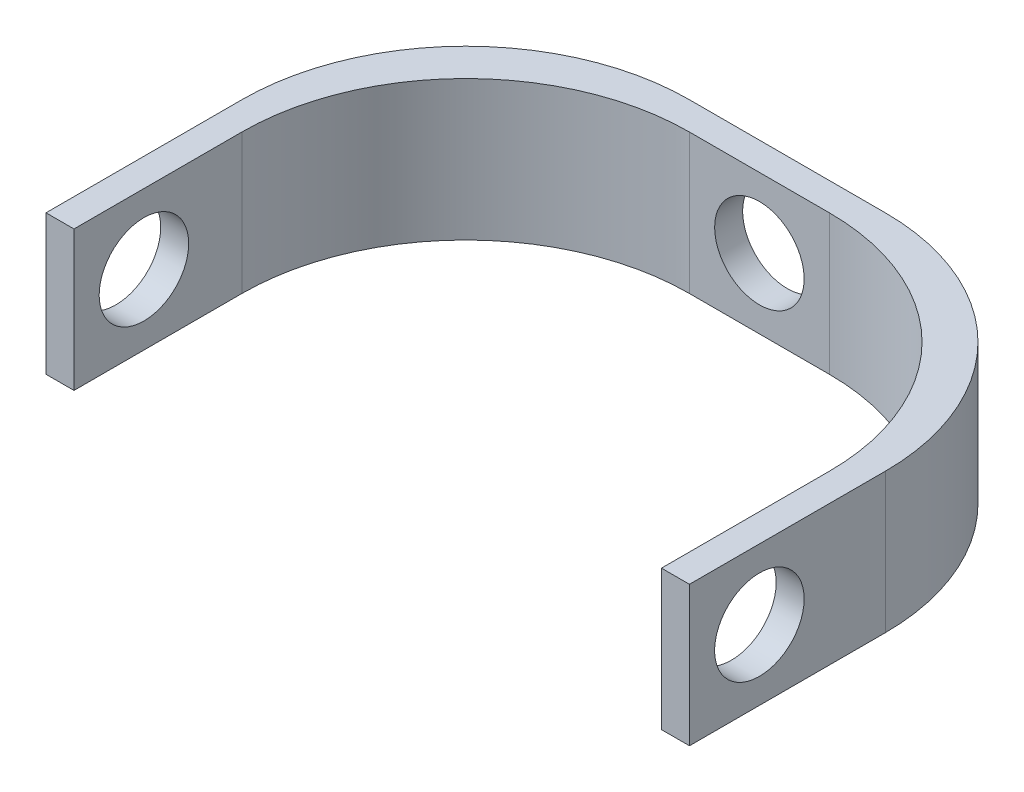
SolidWorks part; units mm, degrees
ref_plane "Front Plane" through (0, 0, 0) normal (0, 0, 1) x (1, 0, 0)
ref_plane "Top Plane" through (0, 0, 0) normal (0, 1, 0) x (1, 0, 0)
ref_plane "Right Plane" through (0, 0, 0) normal (1, 0, 0) x (0, 0, -1)
sketch "Sketch1" plane through (0, 0, 0) normal (0, 1, 0) x (1, 0, 0)
  line L0 (0, 0) -> (1, 0)
  line L1 (0, 0) -> (0, 15)
  line L2 (22, 0) -> (23, 0)
  line L3 (23, 0) -> (23, 15)
  line L4 (1, 14) -> (1, 0)
  line L5 (22, 14) -> (22, 0)
  line L6 (0, 15) -> (23, 15)
  line L7 (1, 14) -> (22, 14)
extrude "Boss-Extrude1" add sketch "Sketch1" along normal blind 5
sketch "Sketch2" plane through (0, 0, -15) normal (0, 0, -1) x (-1, 0, 0)
  circle A0 centre (-11.5, 2.5) radius 1.6
extrude "Cut-Extrude1" cut sketch "Sketch2" against normal blind 5
sketch "Sketch3" plane through (23, 0, 0) normal (1, 0, 0) x (0, 0, -1)
  line L0 (0, 5) -> (5, 5)
  line L1 (0, 5) -> (15, 5) construction
  circle A0 centre (2.5, 2.5) radius 1.6
extrude "Cut-Extrude2" cut sketch "Sketch3" against normal blind 27 contours A0
fillet "Fillet1" radius 8 4 edges at (23, 2.5, -15) (0, 2.5, -15) (1, 2.5, -14) (22, 2.5, -14)
